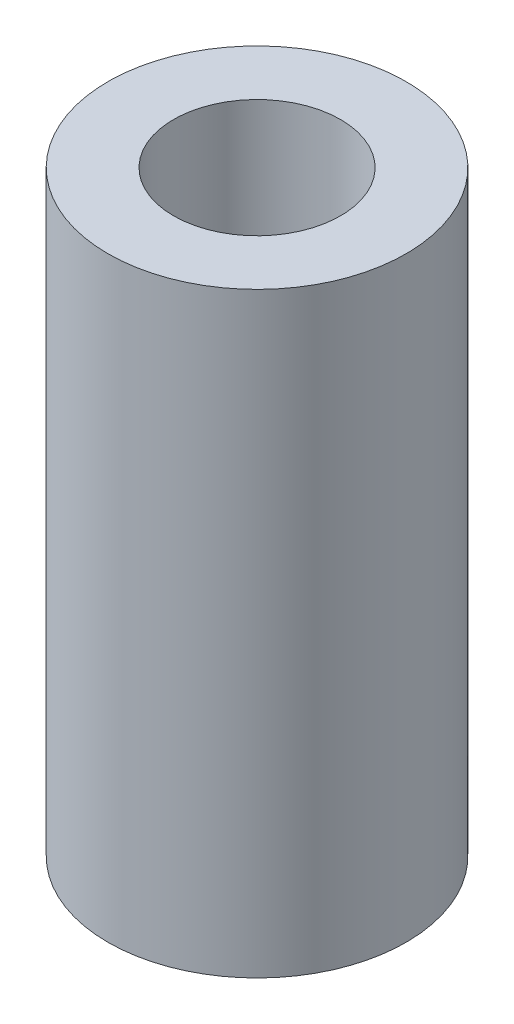
SolidWorks part; units mm, degrees
ref_plane "Front Plane" through (0, 0, 0) normal (0, 0, 1) x (1, 0, 0)
ref_plane "Top Plane" through (0, 0, 0) normal (0, 1, 0) x (1, 0, 0)
ref_plane "Right Plane" through (0, 0, 0) normal (1, 0, 0) x (0, 0, -1)
sketch "Sketch1" plane through (0, 0, 0) normal (0, 1, 0) x (1, 0, 0)
  circle A0 centre (0, 0) radius 2.5
  circle A1 centre (0, 0) radius 1.4
  dimension "D1" = 5
  dimension "D2" = 2.8
extrude "Boss-Extrude1" add sketch "Sketch1" along normal blind 10
